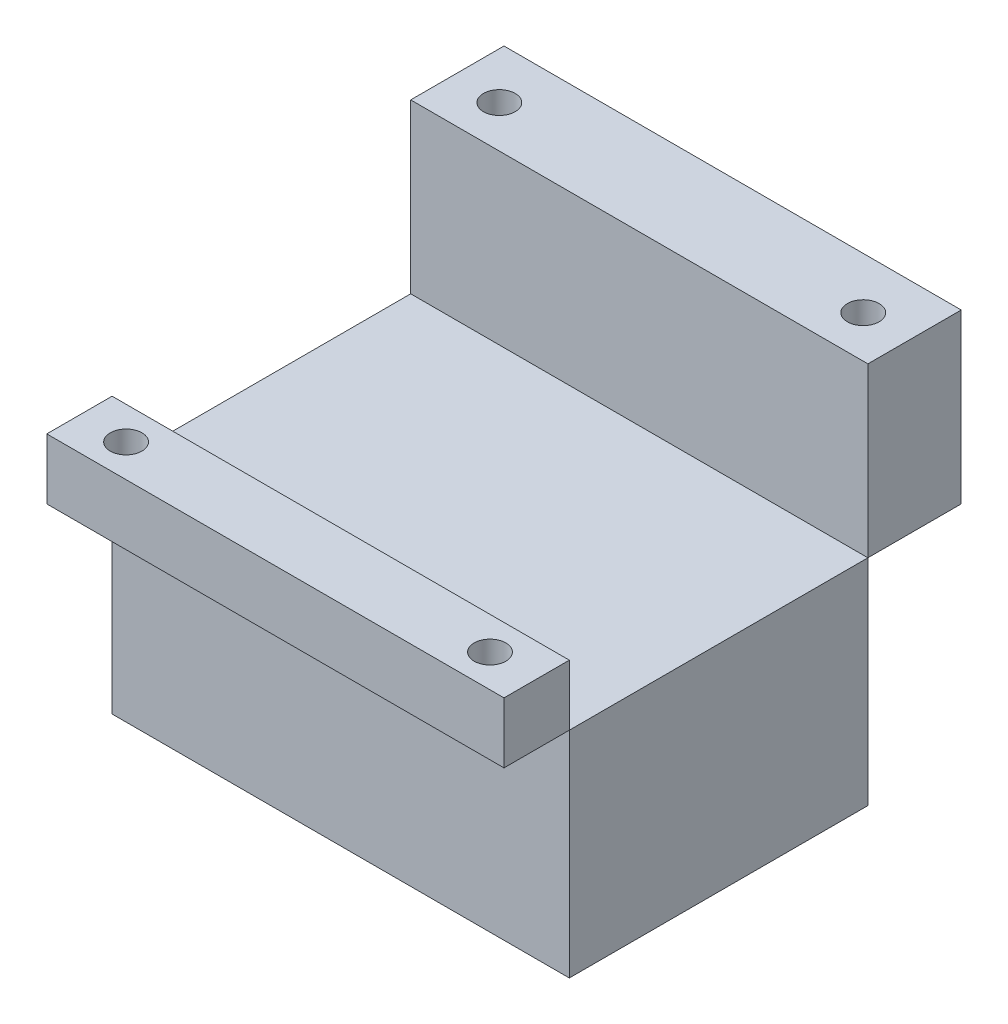
SolidWorks part; units mm, degrees
ref_plane "前基準面" through (0, 0, 0) normal (0, 0, 1) x (1, 0, 0)
ref_plane "上基準面" through (0, 0, 0) normal (0, 1, 0) x (1, 0, 0)
ref_plane "右基準面" through (0, 0, 0) normal (1, 0, 0) x (0, 0, -1)
sketch "草圖1" plane through (0, 0, 0) normal (0, 1, 0) x (1, 0, 0)
  line L1 (-24.5, 16) -> (24.5, 16)
  line L2 (-24.5, 16) -> (-24.5, -16)
  line L3 (-24.5, -16) -> (24.5, -16)
  line L4 (24.5, 16) -> (24.5, -16)
  line L5 (0, -16) -> (0, 16) construction
  line L6 (-24.5, 0) -> (24.5, 0) construction
  point P0 (0, 0)
extrude "填料-伸長1" add sketch "草圖1" along normal blind 23
sketch "草圖7" plane through (0, 23, 0) normal (0, 1, 0) x (1, 0, 0)
  line L1 (24.5, -16) -> (-24.5, -16)
  line L2 (24.5, -16) -> (24.5, -23)
  line L3 (24.5, -23) -> (-24.5, -23)
  line L4 (-24.5, -16) -> (-24.5, -23)
  point P5 (0, 0)
  point P6 (-24.5, -16)
  dimension "D1" = 7
extrude "填料-伸長4" add sketch "草圖7" along normal blind 6.5 separate body
sketch "草圖8" plane through (0, 23, 0) normal (0, 1, 0) x (1, 0, 0)
  line L1 (-24.5, 16) -> (24.5, 16)
  line L2 (-24.5, 16) -> (-24.5, 26)
  line L3 (-24.5, 26) -> (24.5, 26)
  line L4 (24.5, 16) -> (24.5, 26)
  point P5 (24.5, 16)
  dimension "D1" = 10
extrude "填料-伸長5" add sketch "草圖8" along normal blind 18 separate body
sketch "草圖10" plane through (0, 23, 0) normal (0, -1, 0) x (1, 0, 0)
  line L0 (24.5, -26) -> (-24.5, -26) construction
  line L1 (24.5, -16) -> (24.5, -26) construction
  line L2 (-24.5, -26) -> (-24.5, -16) construction
  circle A0 centre (-19.5, -20.5) radius 1.7
  circle A1 centre (19.5, -20.5) radius 1.7
  dimension "D1" = 5.5
  dimension "D2" = 5
  dimension "D3" = 5.5
  dimension "D4" = 5
extrude "除料-伸長1" cut sketch "草圖10" against normal through all
sketch "草圖11" plane through (0, 23, 0) normal (0, -1, 0) x (1, 0, 0)
  line L0 (-24.5, 23) -> (24.5, 23) construction
  line L1 (24.5, 23) -> (24.5, 16) construction
  line L2 (-24.5, 16) -> (-24.5, 23) construction
  circle A0 centre (19.5, 19.5) radius 1.7
  circle A1 centre (-19.5, 19.5) radius 1.7
  point P8 (16.8674, 20.3415)
  point P9 (0, 0)
  dimension "D1" = 3.5
  dimension "D3" = 3.4
  dimension "D2" = 5
  dimension "D4" = 5
  dimension "D5" = 3.5
extrude "除料-伸長2" cut sketch "草圖11" against normal through all
